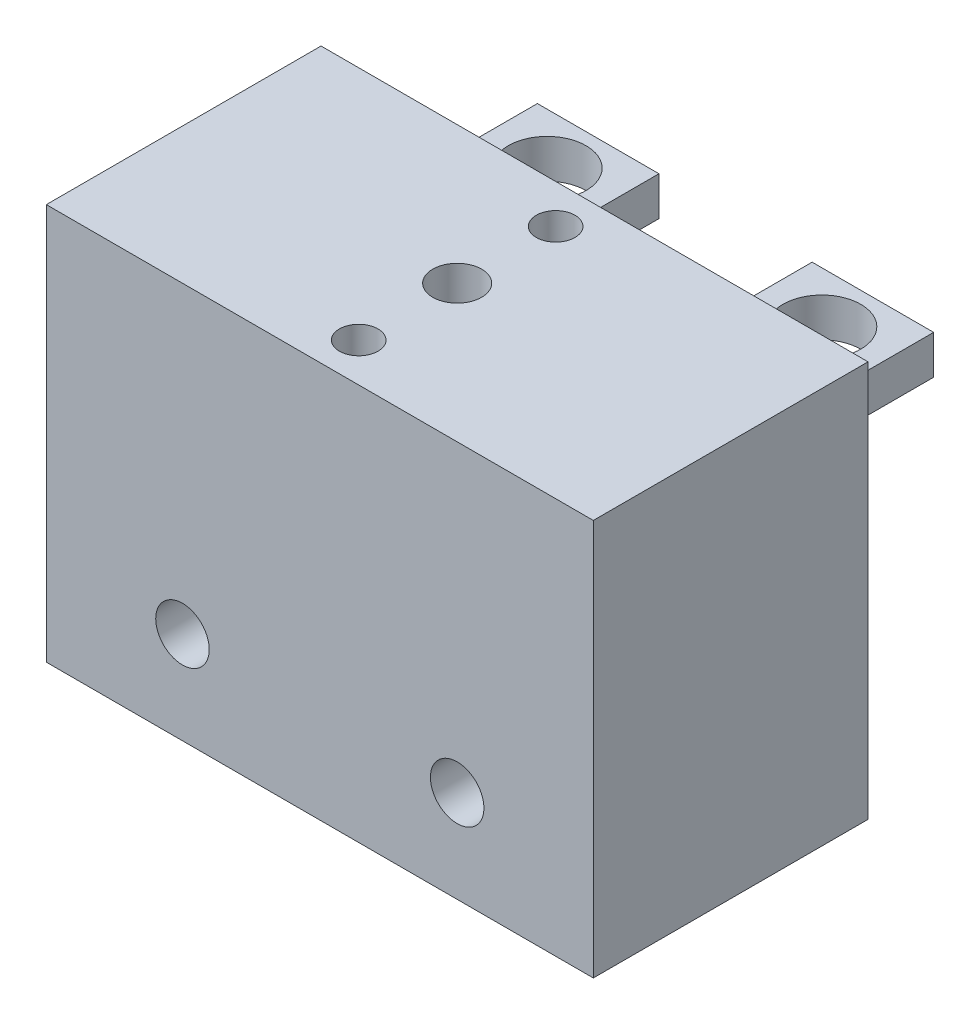
SolidWorks part; units mm, degrees
ref_plane "Front Plane" through (0, 0, 0) normal (0, 0, 1) x (1, 0, 0)
ref_plane "Top Plane" through (0, 0, 0) normal (0, 1, 0) x (1, 0, 0)
ref_plane "Right Plane" through (0, 0, 0) normal (1, 0, 0) x (0, 0, -1)
sketch "Sketch1" plane through (0, 0, 0) normal (0, 1, 0) x (1, 0, 0)
  line L1 (0, 0) -> (57.15, 0)
  line L2 (0, 0) -> (0, 28.702)
  line L3 (0, 28.702) -> (57.15, 28.702)
  line L4 (57.15, 0) -> (57.15, 28.702)
  dimension "D1" = 28.702
  dimension "D2" = 57.15
extrude "Extrude1" add sketch "Sketch1" along normal blind 41.402
sketch "Sketch2" plane through (0, 41.402, 0) normal (0, 1, 0) x (-1, 0, 0)
  line L0 (-57.15, -14.351) -> (0, -14.351) construction
  line L1 (-57.15, 0) -> (-57.15, -28.702) construction
  line L2 (0, -28.702) -> (0, 0) construction
  line L3 (-28.575, -28.702) -> (-28.575, 0) construction
  line L4 (-57.15, -28.702) -> (0, -28.702) construction
  line L5 (0, 0) -> (-57.15, 0) construction
  circle A0 centre (-28.575, -14.351) radius 2.5527
  dimension "D1" = 5.1054
extrude "Cut-Extrude1" cut sketch "Sketch2" against normal through all
sketch "Sketch3" plane through (0, 41.402, 0) normal (0, 1, 0) x (-1, 0, 0)
  line L0 (-28.575, -28.702) -> (-28.575, 0) construction
  line L1 (-57.15, -28.702) -> (0, -28.702) construction
  line L2 (0, 0) -> (-57.15, 0) construction
  circle A0 centre (-28.575, -24.638) radius 2.0193
  circle A1 centre (-28.575, -4.064) radius 2.0193
  dimension "D3" = 4.0386
  dimension "D4" = 4.0386
  dimension "D1" = 4.064
  dimension "D2" = 24.638
extrude "Cut-Extrude2" cut sketch "Sketch3" against normal blind 25.4
sketch "Sketch8" plane through (0, 0, -28.702) normal (0, 0, -1) x (-1, 0, 0)
  line L0 (-57.15, 41.402) -> (-57.15, 0) construction
  line L1 (0, 41.402) -> (0, 0) construction
  line L2 (-57.15, 41.402) -> (0, 41.402) construction
  circle A0 centre (-42.926, 9.652) radius 2.794
  circle A1 centre (-14.224, 9.652) radius 2.794
  dimension "D1" = 5.588
  dimension "D2" = 5.588
  dimension "D3" = 14.224
  dimension "D4" = 14.224
  dimension "D5" = 31.75
  dimension "D6" = 31.75
extrude "Cut-Extrude3" cut sketch "Sketch8" against normal through all
sketch "Sketch9" plane through (0, 0, -28.702) normal (0, 0, -1) x (-1, 0, 0)
  line L1 (-49.276, 32.766) -> (-36.576, 32.766)
  line L2 (-49.276, 32.766) -> (-49.276, 28.702)
  line L3 (-49.276, 28.702) -> (-36.576, 28.702)
  line L4 (-36.576, 32.766) -> (-36.576, 28.702)
  line L5 (-20.574, 32.766) -> (-7.874, 32.766)
  line L6 (-20.574, 32.766) -> (-20.574, 28.702)
  line L7 (-20.574, 28.702) -> (-7.874, 28.702)
  line L8 (-7.874, 32.766) -> (-7.874, 28.702)
  line L10 (-57.15, 41.402) -> (0, 41.402) construction
  line L11 (-57.15, 41.402) -> (-57.15, 0) construction
  point P8 (-42.926, 32.766)
  point P10 (-14.224, 32.766)
  dimension "D1" = 4.064
  dimension "D2" = 4.064
  dimension "D3" = 12.7
  dimension "D4" = 12.7
  dimension "D5" = 14.224
  dimension "D6" = 42.926
  dimension "D7" = 8.636
  dimension "D8" = 8.636
extrude "Extrude2" add sketch "Sketch9" along normal blind 14.732
sketch "Sketch10" plane through (0, 32.766, 0) normal (0, 1, 0) x (-1, 0, 0)
  line L0 (-57.15, 0) -> (-57.15, -28.702) construction
  line L1 (0, 0) -> (-57.15, 0) construction
  circle A0 centre (-42.926, -38.1) radius 4.064
  circle A1 centre (-14.224, -38.1) radius 4.064
  dimension "D1" = 8.128
  dimension "D2" = 8.128
  dimension "D3" = 14.224
  dimension "D4" = 42.926
  dimension "D5" = 38.1
  dimension "D6" = 38.1
extrude "Cut-Extrude4" cut sketch "Sketch10" against normal through all
